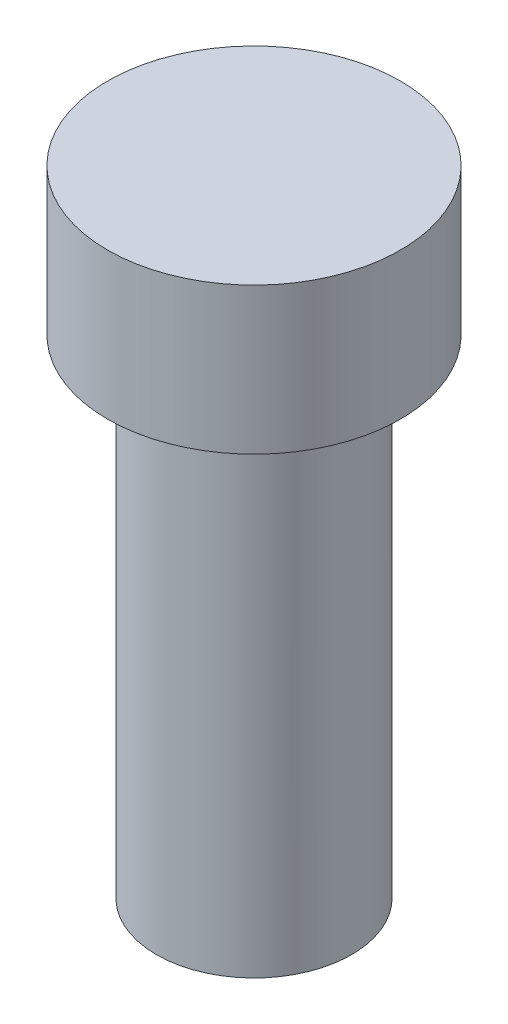
SolidWorks part; units mm, degrees
ref_plane "Front Plane" through (0, 0, 0) normal (0, 0, 1) x (1, 0, 0)
ref_plane "Top Plane" through (0, 0, 0) normal (0, 1, 0) x (1, 0, 0)
ref_plane "Right Plane" through (0, 0, 0) normal (1, 0, 0) x (0, 0, -1)
sketch "Sketch1" plane through (0, 0, 0) normal (0, 1, 0) x (1, 0, 0)
  circle A0 centre (0, 0) radius 3
  dimension "D1" = 6
extrude "Boss-Extrude1" add sketch "Sketch1" along normal blind 3
sketch "Sketch2" plane through (0, 0, 0) normal (0, -1, 0) x (1, 0, 0)
  circle A0 centre (0, 0) radius 2
  dimension "D1" = 4
extrude "Boss-Extrude2" add sketch "Sketch2" along normal blind 10
